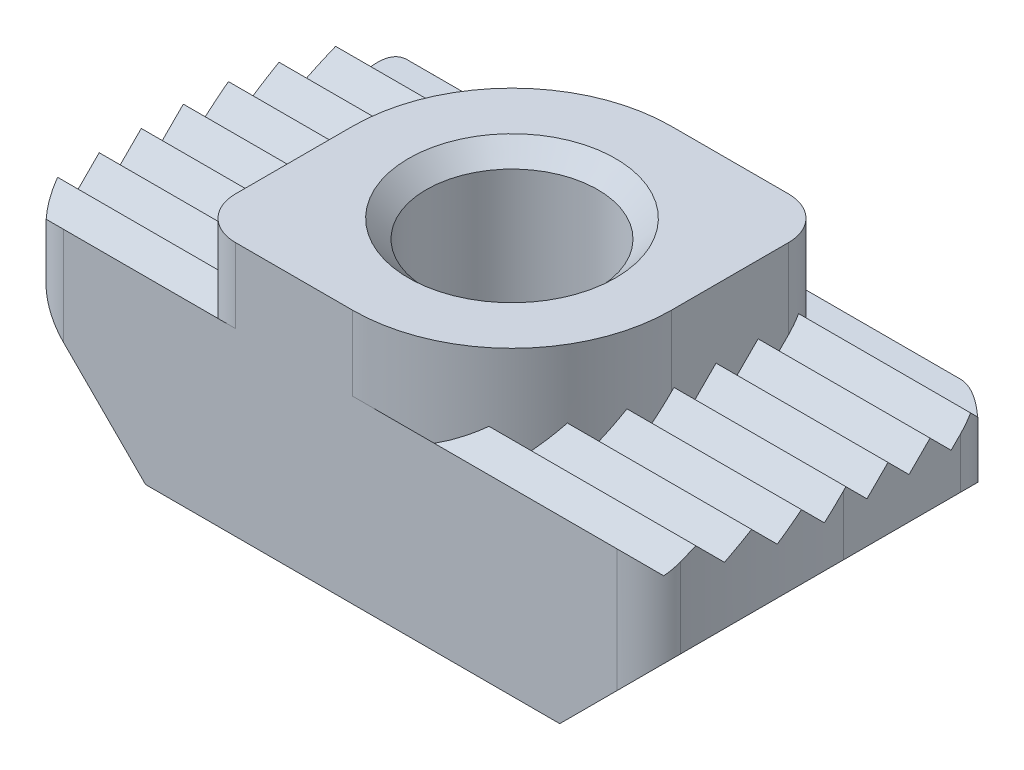
SolidWorks part; units mm, degrees
ref_plane "Front Plane" through (0, 0, 0) normal (0, 0, 1) x (1, 0, 0)
ref_plane "Top Plane" through (0, 0, 0) normal (0, 1, 0) x (1, 0, 0)
ref_plane "Right Plane" through (0, 0, 0) normal (1, 0, 0) x (0, 0, -1)
ref_plane "Plane1" through (0, 0, 0) normal (1, 0, 0) x (0, 0, -1)
sketch "Sketch1" plane through (0, 0, 0) normal (1, 0, 0) x (0, 0, -1)
  line L0 (-3.8481, 4.3485) -> (-3.8481, 0)
  line L1 (-3.8481, 0) -> (3.8481, 0)
  line L2 (3.8481, 0) -> (3.8481, 4.3485)
  line L3 (3.8481, 4.3485) -> (3.6195, 3.9929)
  line L4 (3.6195, 3.9929) -> (3.1115, 4.5009)
  line L5 (3.1115, 4.5009) -> (2.6035, 3.9929)
  line L6 (2.6035, 3.9929) -> (2.0955, 4.5009)
  line L7 (2.0955, 4.5009) -> (1.5875, 3.9929)
  line L8 (1.5875, 3.9929) -> (1.0795, 4.5009)
  line L9 (1.0795, 4.5009) -> (0.5715, 3.9929)
  line L10 (0.5715, 3.9929) -> (0.0635, 4.5009)
  line L11 (0.0635, 4.5009) -> (-0.4445, 3.9929)
  line L12 (-0.4445, 3.9929) -> (-0.9525, 4.5009)
  line L13 (-0.9525, 4.5009) -> (-1.4605, 3.9929)
  line L14 (-1.4605, 3.9929) -> (-1.9685, 4.5009)
  line L15 (-1.9685, 4.5009) -> (-2.4765, 3.9929)
  line L16 (-2.4765, 3.9929) -> (-2.9845, 4.5009)
  line L17 (-2.9845, 4.5009) -> (-3.4925, 3.9929)
  line L18 (-3.4925, 3.9929) -> (-3.8481, 4.3485)
extrude "Boss-Extrude1" add sketch "Sketch1" against normal mid plane 16.002
ref_plane "Plane2" through (0, 0, 0) normal (0, 0, 1) x (1, 0, 0)
sketch "Sketch2" plane through (0, 0, 0) normal (0, 0, 1) x (1, 0, 0)
  line L0 (-10.541, 2.9997) -> (-10.541, -2.9997)
  line L1 (-10.541, -2.9997) -> (0, -2.9997)
  line L2 (0, -2.9997) -> (0, 0)
  line L3 (0, 0) -> (-5.0013, 0)
  line L4 (-5.0013, 0) -> (-8.001, 2.9997)
  line L5 (-8.001, 2.9997) -> (-10.541, 2.9997)
extrude "Cut-Extrude1" cut sketch "Sketch2" against normal mid plane 15.3924
ref_plane "Plane3" through (0, 0, 0) normal (0, 0, 1) x (1, 0, 0)
ref_plane "Plane4" through (0, 0, 0) normal (0, 0, 1) x (1, 0, 0)
sketch "Sketch4" plane through (0, 0, 0) normal (0, 0, 1) x (1, 0, 0)
  line L0 (0, 0) -> (0, -2.9997)
  line L1 (0, -2.9997) -> (-10.541, -2.9997)
  line L2 (-10.541, -2.9997) -> (-10.541, 5.5397)
  line L3 (-10.541, 5.5397) -> (-5.0013, 0)
  line L4 (-5.0013, 0) -> (0, 0)
ref_plane "Plane5" through (0, 0, 0) normal (0, 0, 1) x (1, 0, 0)
sketch "Sketch5" plane through (0, 0, 0) normal (0, 0, 1) x (1, 0, 0)
  line L0 (0, 0) -> (0, -2.9997)
  line L1 (0, -2.9997) -> (10.541, -2.9997)
  line L2 (10.541, -2.9997) -> (10.541, 2.9997)
  line L3 (10.541, 2.9997) -> (8.001, 2.9997)
  line L4 (8.001, 2.9997) -> (5.0013, 0)
  line L5 (5.0013, 0) -> (0, 0)
extrude "Cut-Extrude2" cut sketch "Sketch5" against normal mid plane 15.3924
ref_plane "Plane6" through (0, 0, 0) normal (0, 0, 1) x (1, 0, 0)
ref_plane "Plane7" through (0, 0, 0) normal (0, 0, 1) x (1, 0, 0)
sketch "Sketch7" plane through (0, 0, 0) normal (0, 0, 1) x (1, 0, 0)
  line L0 (0, -2.9997) -> (0, 0)
  line L1 (0, 0) -> (5.0013, 0)
  line L2 (5.0013, 0) -> (10.541, 5.5397)
  line L3 (10.541, 5.5397) -> (10.541, -2.9997)
  line L4 (10.541, -2.9997) -> (0, -2.9997)
ref_plane "Plane8" through (0, 0, 0) normal (0, 1, 0) x (1, 0, 0)
sketch "Sketch8" plane through (0, 0, 0) normal (0, 1, 0) x (1, 0, 0)
  line L0 (-16.002, 7.6962) -> (-16.002, -7.6962)
  line L1 (-16.002, -7.6962) -> (16.002, -7.6962)
  line L2 (16.002, -7.6962) -> (16.002, 7.6962)
  line L3 (16.002, 7.6962) -> (-16.002, 7.6962)
  line L4 (-6.985, -3.8481) -> (6.3851, -3.8481)
  line L5 (8.001, 0) -> (8.001, 2.8321)
  line L6 (6.985, 3.8481) -> (-6.3851, 3.8481)
  line L7 (-8.001, 0) -> (-8.001, -2.8321)
  arc A0 (-8.001, -2.8321) -> (-6.985, -3.8481) centre (-6.985, -2.8321) ccw
  arc A1 (6.3851, -3.8481) -> (7.3138, -3.244) centre (6.3851, -2.8321) ccw
  arc A2 (7.3138, -3.244) -> (8.001, 0) centre (0, 0) ccw
  arc A3 (8.001, 2.8321) -> (6.985, 3.8481) centre (6.985, 2.8321) ccw
  arc A4 (-6.3851, 3.8481) -> (-7.3138, 3.244) centre (-6.3851, 2.8321) ccw
  arc A5 (-7.3138, 3.244) -> (-8.001, 0) centre (0, 0) ccw
extrude "Cut-Extrude3" cut sketch "Sketch8" along normal blind 7.6962
ref_plane "Plane9" through (0, 6.1468, 0) normal (0, 1, 0) x (1, 0, 0)
sketch "Sketch9" plane through (0, 6.1468, 0) normal (0, 1, 0) x (1, 0, 0)
  line L0 (-2.8321, -3.8481) -> (0, -3.8481)
  line L1 (3.8481, 0) -> (3.8481, 2.8321)
  line L2 (2.8321, 3.8481) -> (0, 3.8481)
  line L3 (-3.8481, 0) -> (-3.8481, -2.8321)
  arc A0 (-3.8481, -2.8321) -> (-2.8321, -3.8481) centre (-2.8321, -2.8321) ccw
  arc A1 (0, -3.8481) -> (3.8481, 0) centre (0, 0) ccw
  arc A2 (3.8481, 2.8321) -> (2.8321, 3.8481) centre (2.8321, 2.8321) ccw
  arc A3 (0, 3.8481) -> (-3.8481, 0) centre (0, 0) ccw
extrude "Boss-Extrude2" add sketch "Sketch9" against normal blind 3.0734
ref_plane "Plane10" through (0, 6.1468, 0) normal (0, 0, 1) x (-1, 0, 0)
sketch "Sketch10" plane through (0, 6.1468, 0) normal (0, 0, 1) x (-1, 0, 0)
  line L0 (0, 0) -> (2.5, 0)
  line L1 (2.5, 0) -> (2.067, 0.433)
  line L2 (2.067, 0.433) -> (2.067, 5.7138)
  line L3 (2.067, 5.7138) -> (2.5, 6.1468)
  line L4 (2.5, 6.1468) -> (0, 6.1468)
  line L5 (0, 6.1468) -> (0, 0)
  line L6 (0, -0.3073) -> (0, 6.4541) construction
revolve "Cut-Revolve1" cut sketch "Sketch10" angle 360 about L6
